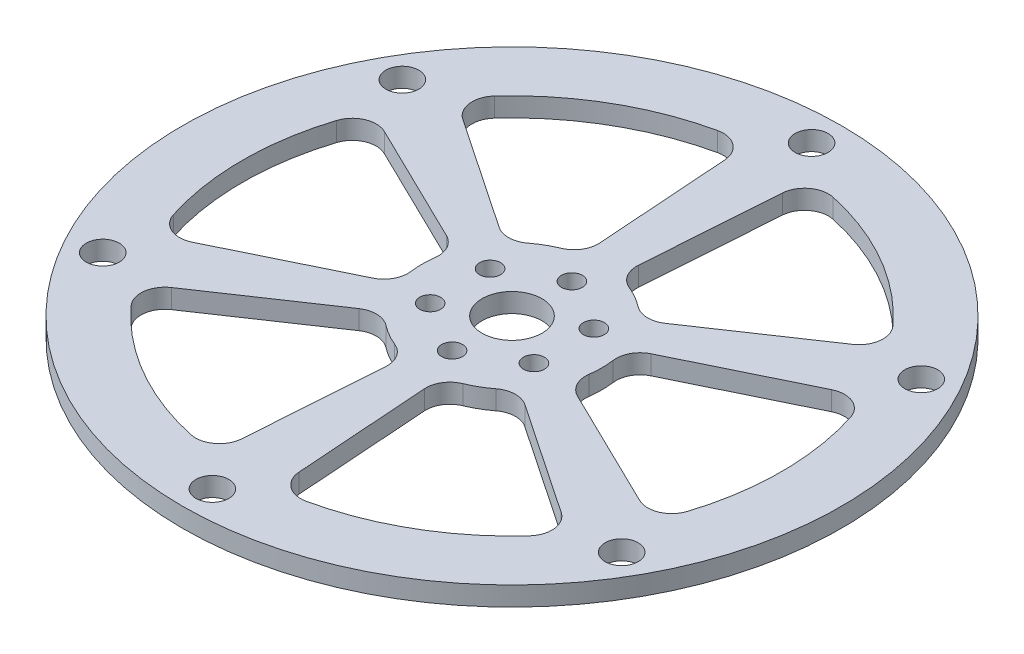
SolidWorks part; units mm, degrees
material "Stainless Steel (ferritic)"
ref_plane "Front Plane" through (0, 0, 0) normal (0, 0, 1) x (1, 0, 0)
ref_plane "Top Plane" through (0, 0, 0) normal (0, 1, 0) x (1, 0, 0)
ref_plane "Right Plane" through (0, 0, 0) normal (1, 0, 0) x (0, 0, -1)
sketch "Sketch1" plane through (0, 0, 0) normal (0, 1, 0) x (1, 0, 0)
  circle A0 centre (0, 0) radius 10 construction
  circle A2 centre (0, 0) radius 15
  circle A3 centre (0, 0) radius 5
  dimension "D1" = 20
  dimension "D3" = 5
extrude "Boss-Extrude1" add sketch "Sketch1" along normal blind 3.2
sketch "Sketch2" plane through (0, 0, 0) normal (0, 1, 0) x (1, 0, 0)
  circle A0 centre (0, 0) radius 50 construction
  circle A1 centre (0, 0) radius 45
  circle A2 centre (0, 0) radius 55
  dimension "D3" = 100
  dimension "D1" = 5
extrude "Boss-Extrude2" add sketch "Sketch2" along normal blind 3.2 separate body
sketch "Sketch5" plane through (0, 0, 0) normal (0, 1, 0) x (1, 0, 0)
  line L0 (0, 96.6167) -> (0, -103.046) construction
  line L1 (-5.0987, 44.7102) -> (-3, 14.6969)
  line L2 (5.0987, 44.7102) -> (3, 14.6969)
  circle A0 centre (0, 0) radius 15 construction
  circle A1 centre (0, 0) radius 45 construction
  arc A2 (3, 14.6969) -> (-3, 14.6969) centre (0, 0) ccw
  arc A3 (5.0987, 44.7102) -> (-5.0987, 44.7102) centre (0, 0) ccw
  arc A4 (-5.0987, 44.7102) -> (0, -45) centre (0, 0) ccw construction
  arc A5 (-3, 14.6969) -> (0, -15) centre (0, 0) ccw construction
  arc A6 (0, -15) -> (3, 14.6969) centre (0, 0) ccw construction
  arc A7 (0, -45) -> (5.0987, 44.7102) centre (0, 0) ccw construction
  dimension "D1" = 3
  dimension "D2" = 3
  dimension "D3" = 4
  dimension "D4" = 4
extrude "Boss-Extrude3" add sketch "Sketch5" along normal blind 3.2
sketch "Sketch3" plane through (0, 0, 0) normal (0, 1, 0) x (1, 0, 0)
  circle A0 centre (0, 10) radius 1.75
  dimension "D1" = 3.5
  dimension "D2" = 10
extrude "Cut-Extrude2" cut sketch "Sketch3" along normal through all
sketch "Sketch4" plane through (0, 0, 0) normal (0, 1, 0) x (1, 0, 0)
  circle A0 centre (0, 50) radius 2.75
  dimension "D1" = 5.5
  dimension "D2" = 50
extrude "Cut-Extrude3" cut sketch "Sketch4" along normal through all
fillet "Fillet1" radius 4 4 edges at (5.0987, 1.6, -44.7102) (3, 1.6, -14.6969) (-3, 1.6, -14.6969) (-5.0987, 1.6, -44.7102)
pattern_circular "CirPattern1" count 6 over 360 about axis through (0, 0, 0) along (0, 1, 0) of "Boss-Extrude3", "Cut-Extrude3", "Fillet1"
pattern_circular "CirPattern2" count 6 over 360 about axis through (0, 0, 0) along (0, 1, 0) of "Cut-Extrude2"
equation "\"flywheel_mounting_hole_circle_diameter\"= 100mm"
equation "\"motor_shaft_mounting_hole_circle_diameter\"= 20mm"
equation "\"ring_width\"= 10mm"
equation "\"material_thickness\"= 3.2mm"
equation "\"D1@Sketch1\"=\"motor_shaft_mounting_hole_circle_diameter\""
equation "\"D2@Sketch1\"=\"ring_width\"/2"
equation "\"D3@Sketch1\"=\"ring_width\"/2"
equation "\"D1@Boss-Extrude1\"=\"material_thickness\""
equation "\"D1@Sketch2\"=\"ring_width\"/2"
equation "\"D2@Sketch2\"=\"ring_width\"/2"
equation "\"D3@Sketch2\"=\"flywheel_mounting_hole_circle_diameter\""
equation "\"D1@Boss-Extrude2\"=\"material_thickness\""
equation "\"D2@Sketch3\"=\"motor_shaft_mounting_hole_circle_diameter\"/2"
equation "\"D2@Sketch4\"=\"flywheel_mounting_hole_circle_diameter\"/2"
equation "\"D4@Sketch5\"=\"D3@Sketch5\""
equation "\"D1@Boss-Extrude3\"=\"material_thickness\""
